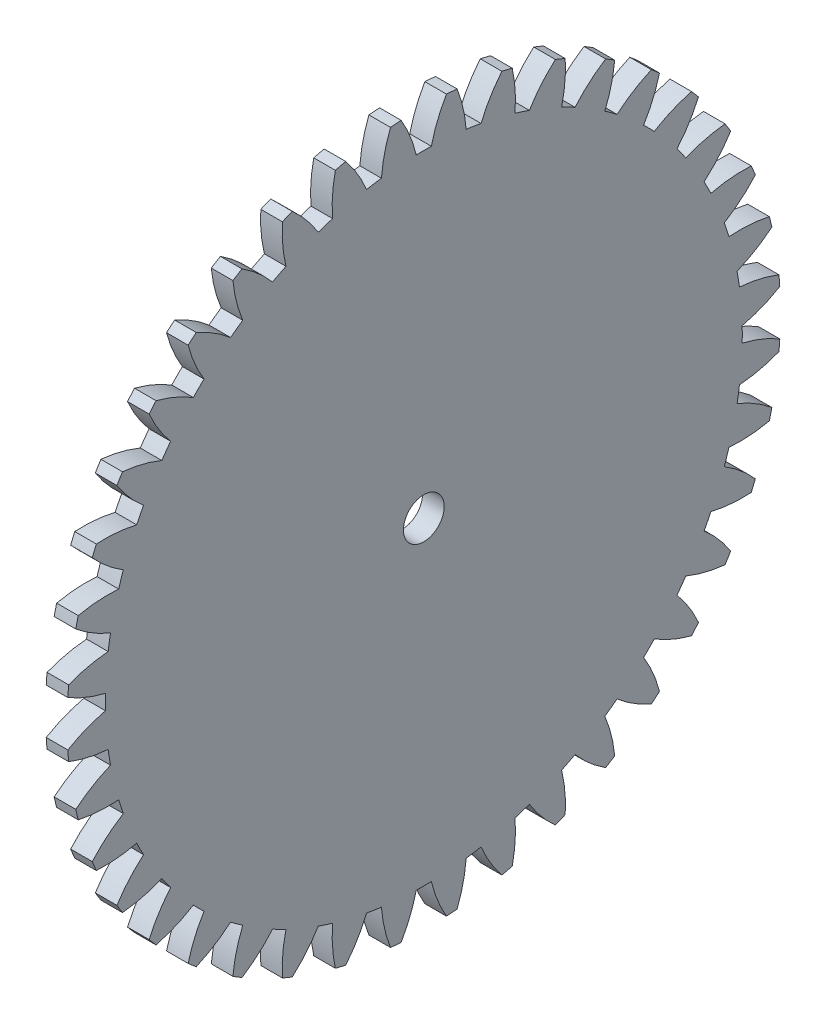
SolidWorks part; units mm, degrees
ref_plane "Plane1" through (0, 0, 0) normal (0, 0, 1) x (1, 0, 0)
ref_plane "Plane2" through (0, 0, 0) normal (0, 1, 0) x (1, 0, 0)
ref_plane "Plane3" through (0, 0, 0) normal (1, 0, 0) x (0, 0, -1)
other "Configuration Table"
sketch "HoldingSke" plane through (0, 0, 0) normal (0, 1, 0) x (1, 0, 0)
  line L0 (0, 0) -> (0.3064, -0.2571)
  line L1 (-15, 0) -> (100, 0) construction
  line L2 (0, 0) -> (-2.1039, 2.3779)
  line L3 (0, 0) -> (-11.863, 4.5341)
  line L4 (0, 0) -> (6.6156, 5.5511)
  line L5 (0, 0) -> (-46.8476, -17.4728)
  line L6 (0, 0) -> (-2.6361, -1.7786)
  line L7 (-2.1039, 2.3779) -> (8.6586, 51.2059)
  line L8 (-76.2, 54.61) -> (-75.2, 54.61)
  line L9 (-71.009, 38.7566) -> (-53.1078, 45.2721)
  line L10 (-76.2, 71.12) -> (104.1128, 71.12)
  line L11 (0, 0) -> (-3.18, 0)
  line L12 (-76.2, 101.6) -> (-76.113, 101.6)
  line L13 (24.9733, 27.94) -> (52.9518, 28.4284)
  line L14 (24.9733, 27.94) -> (24.9743, 27.94)
  line L15 (24.9733, 27.94) -> (100.4006, 29.5858)
  line L16 (-63.627, -2.5) -> (-12.827, -2.5)
  circle A0 centre (0, 0) radius 3
  circle A1 centre (0, 0) radius 37.5
  circle A2 centre (0, 0) radius 37.5
  circle A3 centre (0, 0) radius 3
  dimension "MHD" = 75
  dimension "Hub_dia" = 75
  dimension "Bore" = 6
  dimension "MBD" = 6
  dimension "Num_teeth" = 40
  dimension "Pitch" = 0.4
  dimension "Overall_len" = 50
  dimension "Show_teeth" = 40
  dimension "Thickness" = 3.18
  dimension "OAL" = 50.0001
  dimension "T_dim" = 1
  dimension "Ap" = 20
  dimension "H" = 19.05
  dimension "Pitch_radius" = 180.3128
  dimension "Width" = 3.18
  dimension "Backlash" = 0.087
  dimension "Addendum_fac" = 1
  dimension "Dedendum_fac" = 1.25
  dimension "Clearance_fac" = 0.25
  dimension "Dedendum_add" = 0.001
  dimension "Module" = 2.5
sketch "BasProSke" plane through (0, 0, 0) normal (0, 1, 0) x (1, 0, 0)
  line L0 (-10, 0) -> (60, 0) construction
  line L1 (0, 0) -> (0, 52.5)
  line L2 (0, 0) -> (3.18, 0)
  line L3 (3.18, 0) -> (3.18, 52.5)
  line L4 (3.18, 52.5) -> (0, 52.5)
  dimension "Thickness" = 3.18
  dimension "Diameter" = 105
revolve "Base-Revolve" add sketch "BasProSke" angle 360 about L0
sketch "TooCutSke" plane through (0, 0, 0) normal (1, 0, 0) x (0, 0, -1)
  line L1 (0, 0) -> (0, 107) construction
  line L2 (0, 0) -> (-2.1152, 49.9552) construction
  line L3 (0, 0) -> (-7.8408, 99.6263) construction
  line L4 (-2.1152, 49.9552) -> (-3.9204, 49.8132) construction
  arc A0 (1.1089, 46.8609) -> (-1.1089, 46.8609) centre (0, 0) ccw
  arc A1 (3.3504, 52.4184) -> (-3.3504, 52.4184) centre (0, 0) ccw
  circle A2 centre (0, 0) radius 50 construction
  circle A3 centre (0, 0) radius 46.9846 construction
  arc A4 (-1.1089, 46.8609) -> (-3.3504, 52.4184) centre (-20.5685, 42.2432) ccw
  arc A5 (3.3504, 52.4184) -> (1.1089, 46.8609) centre (20.5685, 42.2432) ccw
  dimension "Root_dia" = 93.748
  dimension "Overcut_dia" = 105.0508
  dimension "Pitch_dia" = 100
  dimension "Base_dia" = 93.9693
  dimension "Flank_rad" = 20
  dimension "Half_ang" = 4.5
  dimension "Half_CT" = 1.8107
extrude "ToothCut" cut sketch "TooCutSke" along normal through all
fillet "Breaks" [suppressed] radius 0.05
fillet "RootFillets" [suppressed] radius 0.626
pattern_circular "TeethCuts" count 40 every 9 about axis through (-10, 0, 0) along (1, 0, 0) of "ToothCut", "RootFillets", "Breaks"
sketch "HubNeaOneSke" plane through (0, 0, 0) normal (-1, 0, 0) x (0, 0, 1)
  circle A0 centre (0, 0) radius 37.5
  dimension "Diameter" = 75
extrude "HubNearOne" [suppressed] add sketch "HubNeaOneSke" along normal blind 46.8201
sketch "HubNeaBotSke" plane through (0, 0, 0) normal (-1, 0, 0) x (0, 0, 1)
  circle A0 centre (0, 0) radius 37.5
  dimension "Diameter" = 75
extrude "HubNearBoth" [suppressed] add sketch "HubNeaBotSke" along normal blind 23.41
ref_plane "FarPln" through (3.18, 0, 0) normal (1, 0, 0) x (0, 0, -1)
sketch "HubFarSke" plane through (3.18, 0, 0) normal (1, 0, 0) x (0, 0, -1)
  circle A0 centre (0, 0) radius 37.5
  dimension "Diameter" = 75
extrude "HubFar" [suppressed] add sketch "HubFarSke" along normal blind 23.41
sketch "BorSke" plane through (0, 0, 0) normal (1, 0, 0) x (0, 0, -1)
  circle A0 centre (0, 0) radius 3
  dimension "Diameter" = 6
extrude "Bore" cut sketch "BorSke" along normal mid plane 100.0001
sketch "KeySke" plane through (0, 0, 0) normal (1, 0, 0) x (0, 0, -1)
  line L0 (-1, 0) -> (-1, 4)
  line L1 (-1, 4) -> (1, 4)
  line L2 (1, 4) -> (1, 0)
  line L3 (0, 0) -> (0, 34) construction
  line L4 (-1, 0) -> (1, 0)
  dimension "Offset" = 4
  dimension "Width" = 2
extrude "Keyway" [suppressed] cut sketch "KeySke" along normal mid plane 100.0001
pattern_circular "Keyway2" [suppressed] count 2 every 90 about axis through (-10, 0, 0) along (1, 0, 0)
equation "' \"Module@HoldingSke\" = 6.35"
equation "' \"Num_teeth@HoldingSke\" = 12"
equation "' \"Ap@HoldingSke\" =  20"
equation "' \"Ap@HoldingSke\" = 20"
equation "' \"Width@HoldingSke\" = 0.5 * 25.4"
equation "' \"Hub_dia@HoldingSke\"= 1 * 25.4"
equation "' \"Hub_dia@HoldingSke\" = 1 * 25.4"
equation "' \"Overall_len@HoldingSke\" = 1.0 * 25.4"
equation "' \"Bore@HoldingSke\" = 0.75 * 25.4"
equation "' \"T_dim@HoldingSke\" = 0.1 * 25.4"
equation "' \"Width@KeySke\" = 0.25 * 25.4"
equation "' \"Show_teeth@HoldingSke\" = 13"
equation "' \"Backlash@HoldingSke\" = 0.009 * 25.4"
equation "' \"Addendum_fac@HoldingSke\" = 1.0"
equation "' \"Dedendum_fac@HoldingSke\" = 1.25"
equation "' \"Dedendum_add@HoldingSke\" = 0.00005 * 25.4"
equation "' \"Clearance_fac@HoldingSke\" = 0.25"
equation "\"Pitch@HoldingSke\" = 1 / \"Module@HoldingSke\""
equation "\"Overcut_dia@TooCutSke\" = (\"Num_teeth@HoldingSke\" + 2 * \"Addendum_fac@HoldingSke\") / \"Pitch@HoldingSke\" + 0.002 * 25.4"
equation "\"Pitch_dia@TooCutSke\" = \"Num_teeth@HoldingSke\" / \"Pitch@HoldingSke\""
equation "\"Base_dia@TooCutSke\" = \"Num_teeth@HoldingSke\" / \"Pitch@HoldingSke\" * cos((\"Ap@HoldingSke\"  * 3.14159265 / 180))"
equation "\"Root_dia@TooCutSke\" = (\"Num_teeth@HoldingSke\" + 2) / \"Pitch@HoldingSke\" - 2 * (\"Addendum_fac@HoldingSke\" + \"Dedendum_fac@HoldingSke\") / \"Pitch@HoldingSke\" - \"Dedendum_add@HoldingSke\" * 2"
equation "\"Half_ang@TooCutSke\" = 180 / \"Num_teeth@HoldingSke\""
equation "\"Half_CT@TooCutSke\" = \"Num_teeth@HoldingSke\" / \"Pitch@HoldingSke\" * sin((3.14159265 / 2 / \"Num_teeth@HoldingSke\")) / 2 - 7 * \"Backlash@HoldingSke\" / 4"
equation "\"Flank_rad@TooCutSke\" = \"Num_teeth@HoldingSke\" / \"Pitch@HoldingSke\" / 5"
equation "\"Radius@RootFillets\" = \"Clearance_fac@HoldingSke\" / \"Pitch@HoldingSke\" + \"Dedendum_add@HoldingSke\""
equation "\"Break_rad@Breaks\" = 0.02 / \"Pitch@HoldingSke\""
equation "\"Thickness@HoldingSke\" = \"Width@HoldingSke\""
equation "\"OAL@HoldingSke\" = \"Thickness@HoldingSke\""
equation "\"MHD@HoldingSke\" = (\"Num_teeth@HoldingSke\" + 2) / \"Pitch@HoldingSke\" - 2 * (\"Addendum_fac@HoldingSke\" + \"Dedendum_fac@HoldingSke\")  / \"Pitch@HoldingSke\" - \"Dedendum_add@HoldingSke\" * 2"
equation "\"MBD@HoldingSke\" = (\"Num_teeth@HoldingSke\" + 2) / \"Pitch@HoldingSke\" - 2 * (\"Addendum_fac@HoldingSke\" + \"Dedendum_fac@HoldingSke\")  / \"Pitch@HoldingSke\" - \"Dedendum_add@HoldingSke\" * 2 - 0.002 * 25.4"
equation "\"MHD@HoldingSke\" = ((sgn( \"MHD@HoldingSke\" - \"Hub_dia@HoldingSke\" )-1)*( \"MHD@HoldingSke\" - \"Hub_dia@HoldingSke\" ))/-2+ \"Hub_dia@HoldingSke\""
equation "\"MBD@HoldingSke\" = ((sgn( \"MBD@HoldingSke\" - \"Bore@HoldingSke\" )-1)*( \"MBD@HoldingSke\" - \"Bore@HoldingSke\" ))/-2+ \"Bore@HoldingSke\""
equation "\"OAL@HoldingSke\" = ((sgn( \"OAL@HoldingSke\" - \"Overall_len@HoldingSke\" )+1)*( \"OAL@HoldingSke\" - \"Overall_len@HoldingSke\" ))/2 + \"Overall_len@HoldingSke\" + 0.000002 * 25.4"
equation "\"Num_teeth@TeethCuts\" = int( \"Show_teeth@HoldingSke\" ) + 1"
equation "\"Num_teeth@TeethCuts\" = ((sgn( \"Num_teeth@TeethCuts\" - \"Num_teeth@HoldingSke\" )-1)*( \"Num_teeth@TeethCuts\" - \"Num_teeth@HoldingSke\" ))/-2+ \"Num_teeth@HoldingSke\""
equation "\"Num_teeth@TeethCuts\" = ((sgn( \"Num_teeth@TeethCuts\" - 2.0)+1)*( \"Num_teeth@TeethCuts\" - 2.0))/2 +2.0"
equation "\"Angle@TeethCuts\" = 360.0 / \"Num_teeth@HoldingSke\""
equation "\"Diameter@BasProSke\" = (\"Num_teeth@HoldingSke\" + 2 * \"Addendum_fac@HoldingSke\") / \"Pitch@HoldingSke\""
equation "\"Thickness@BasProSke\"  = \"Thickness@HoldingSke\""
equation "' \"Fillet_rad@BasProSke\" =  \"Thickness@HoldingSke\" * 0.05"
equation "' \"Fillet_rad@BasProSke\" = \"Thickness@HoldingSke\" * 0.05"
equation "\"MHD@HoldingSke\" = ((sgn( \"MHD@HoldingSke\" - \"Root_dia@TooCutSke\" )-1)*( \"MHD@HoldingSke\" - \"Root_dia@TooCutSke\" ))/-2+ \"Root_dia@TooCutSke\""
equation "\"Diameter@HubNeaOneSke\" = \"MHD@HoldingSke\""
equation "\"Length@HubNearOne\" = \"OAL@HoldingSke\" - \"Thickness@BasProSke\""
equation "\"Diameter@HubNeaBotSke\" = \"MHD@HoldingSke\""
equation "\"Length@HubNearBoth\" = ( \"OAL@HoldingSke\" - \"Thickness@BasProSke\" ) / 2.0"
equation "\"Thickness@FarPln\" = \"Thickness@BasProSke\""
equation "\"Diameter@HubFarSke\" = \"MHD@HoldingSke\""
equation "\"Length@HubFar\" = ( \"OAL@HoldingSke\" - \"Thickness@BasProSke\" ) / 2.0"
equation "\"Diameter@BorSke\" = \"MBD@HoldingSke\""
equation "\"D1@Bore\" = \"OAL@HoldingSke\" * 2.0"
equation "\"D1@Keyway\" = \"OAL@HoldingSke\" * 2.0"
equation "\"Offset@KeySke\" = \"T_dim@HoldingSke\" + \"MBD@HoldingSke\" / 2.0"
